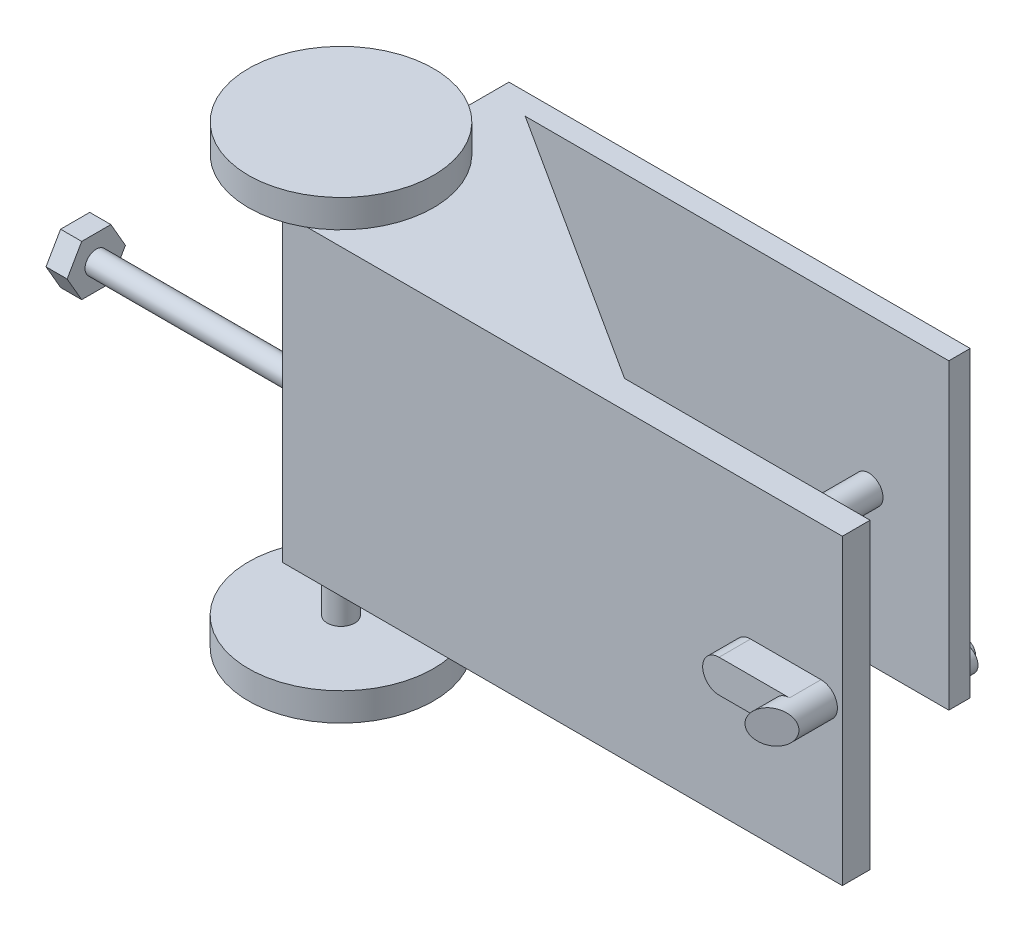
SolidWorks part; units mm, degrees
ref_plane "Plan de face" through (0, 0, 0) normal (0, 0, 1) x (1, 0, 0)
ref_plane "Plan de dessus" through (0, 0, 0) normal (0, 1, 0) x (1, 0, 0)
ref_plane "Plan de droite" through (0, 0, 0) normal (1, 0, 0) x (0, 0, -1)
sketch "Esquisse1" plane through (0, 0, 0) normal (0, 0, 1) x (1, 0, 0)
  line L0 (162.4526, 0) -> (162.4526, 87.2478)
  line L1 (162.4526, 0) -> (0.9932, 0)
  line L2 (162.4526, 87.2478) -> (0.9932, 87.2478)
  line L3 (0.9932, 0) -> (0.9932, 87.2478)
extrude "Boss.-Extru.1" add sketch "Esquisse1" along normal blind 8
sketch "Esquisse8" plane through (0, 87.2478, 0) normal (0, 1, 0) x (1, 0, 0)
  line L0 (0.9932, 0) -> (0.9932, 58.1232)
  line L1 (0.9932, 0) -> (91.6553, 0)
  line L2 (0.9932, 58.1232) -> (91.6553, 58.1232)
  line L3 (91.6553, 0) -> (91.6553, 58.1232)
  line L4 (0.9932, 58.1232) -> (91.6553, 0)
  line L5 (0.9932, 58.1232) -> (32.8752, 107.8536)
  line L6 (91.6553, 0) -> (123.5373, 49.7304)
  line L7 (32.8752, 107.8536) -> (123.5373, 49.7304)
  line M5 (162.4526, 0) -> (0.9932, 0)
extrude "Boss.-Extru.4" add sketch "Esquisse8" against normal blind 8 contours L4 L0 M5
sketch "Esquisse9" plane through (0, 79.2478, 0) normal (0, -1, 0) x (-1, 0, 0)
  line L0 (-0.9932, 58.1232) -> (-91.6553, 0)
  line L1 (-91.6553, 0) -> (-0.9932, 0)
  line L2 (-0.9932, 0) -> (-0.9932, 58.1232)
extrude "Boss.-Extru.5" add sketch "Esquisse9" along normal up to surface (79.2478 mm away) contours L2 L0 L1 up to face at (81.7229, 0, 4)
sketch "Esquisse10" plane through (0.9932, 0, 0) normal (-1, 0, 0) x (0, 0, 1)
  line L0 (0.0289, 80.9428) -> (0.0289, 6.4515)
  line L1 (0.0289, 80.9428) -> (-66.0841, 80.9428)
  line L2 (0.0289, 6.4515) -> (-66.0841, 6.4515)
  line L3 (-66.0841, 80.9428) -> (-66.0841, 6.4515)
extrude "Enlèv. mat.-Extru.2" cut sketch "Esquisse10" against normal blind 96
sketch "Esquisse13" plane through (0.9932, 0, 0) normal (-1, 0, 0) x (0, 0, 1)
  line L0 (-57.3293, 0) -> (-57.3293, 87.2478)
  line L1 (-57.3293, 0) -> (-51.1587, 0)
  line L2 (-57.3293, 87.2478) -> (-51.1587, 87.2478)
  line L3 (-51.1587, 0) -> (-51.1587, 87.2478)
  line L4 (8, 0) -> (-58.1232, 0) construction
  line L5 (8, 87.2478) -> (-58.1232, 87.2478) construction
extrude "Boss.-Extru.6" add sketch "Esquisse13" against normal blind 133 contours L0 L2 L3 L1
sketch "Esquisse16" plane through (0, 0, -57.3293) normal (0, 0, -1) x (-1, 0, 0)
  circle A0 centre (-110.9236, 43.6239) radius 4.0925
  dimension "D1" = 8.185
extrude "Boss.-Extru.8" add sketch "Esquisse16" against normal blind 61.0904
sketch "Esquisse18" plane through (0, 0, -57.3293) normal (0, 0, -1) x (-1, 0, 0)
  line L0 (-128.5715, 5.1557) -> (-108.0869, 5.1557) construction
  line L1 (-128.5715, 8.7286) -> (-108.0869, 8.7286)
  line L2 (-128.5715, 1.5828) -> (-108.0869, 1.5828)
  arc A0 (-128.5715, 8.7286) -> (-128.5715, 1.5828) centre (-128.5715, 5.1557) ccw
  arc A1 (-108.0869, 1.5828) -> (-108.0869, 8.7286) centre (-108.0869, 5.1557) ccw
  point P2 (-118.3292, 5.1557)
extrude "Boss.-Extru.9" add sketch "Esquisse18" along normal blind 4.0904
sketch "Esquisse20" plane through (0, 0, -61.4197) normal (0, 0, -1) x (-1, 0, 0)
  circle A0 centre (-126.4235, 5.1557) radius 2.9502
extrude "Boss.-Extru.11" add sketch "Esquisse20" along normal blind 2.0904
sketch "Esquisse22" plane through (0, 0, -61.4197) normal (0, 0, -1) x (-1, 0, 0)
  circle A0 centre (-119.4027, 5.1557) radius 2.9502
  dimension "D1" = 5.9005
extrude "Boss.-Extru.12" add sketch "Esquisse22" along normal blind 2.0904
sketch "Esquisse23" plane through (0, 0, -61.4197) normal (0, 0, -1) x (-1, 0, 0)
  circle A0 centre (-109.5748, 5.1557) radius 3.3991
extrude "Boss.-Extru.13" add sketch "Esquisse23" along normal blind 4.0904
sketch "Esquisse24" plane through (0, 87.2478, 0) normal (0, 1, 0) x (1, 0, 0)
  circle A0 centre (9.8998, 0) radius 3.9591
  dimension "D1" = 7.9182
extrude "Boss.-Extru.14" add sketch "Esquisse24" along normal blind 15.0904 and the other way blind 100
sketch "Esquisse25" plane through (0, 102.3382, 0) normal (0, 1, 0) x (1, 0, 0)
  circle A0 centre (9.8998, 0) radius 26.6848
  dimension "D1" = 53.3696
extrude "Boss.-Extru.15" add sketch "Esquisse25" along normal blind 8.0904
sketch "Esquisse26" plane through (0, -12.7522, 0) normal (0, -1, 0) x (-1, 0, 0)
  circle A0 centre (-9.8998, 0) radius 26.6848
  dimension "D1" = 53.3696
extrude "Boss.-Extru.16" add sketch "Esquisse26" along normal blind 8.0904
sketch "Esquisse27" plane through (0, 0, 8) normal (0, 0, 1) x (1, 0, 0)
  line L0 (156.3009, 43.6239) -> (135.9971, 43.6239) construction
  line L1 (156.3009, 38.8896) -> (135.9971, 38.8896)
  line L2 (156.3009, 48.3583) -> (135.9971, 48.3583)
  arc A0 (156.3009, 38.8896) -> (156.3009, 48.3583) centre (156.3009, 43.6239) ccw
  arc A1 (135.9971, 48.3583) -> (135.9971, 38.8896) centre (135.9971, 43.6239) ccw
  point P2 (146.149, 43.6239)
extrude "Boss.-Extru.17" add sketch "Esquisse27" along normal blind 9.0904
sketch "Esquisse28" plane through (0.9932, 0, 0) normal (-1, 0, 0) x (0, 0, 1)
  circle A0 centre (3.5623, 43.6972) radius 3.2413
extrude "bolt" add sketch "Esquisse28" along normal blind 58.0904
sketch "Esquisse29" plane through (0, 0, -57.3293) normal (0, 0, -1) x (-1, 0, 0)
  line L0 (-15.9568, 87.2478) -> (-0.9195, 87.2478)
  line L1 (-15.9568, 87.2478) -> (-15.9568, -8.0839)
  line L2 (-0.9195, 87.2478) -> (-0.9195, -8.0839)
  line L3 (-15.9568, -8.0839) -> (-0.9195, -8.0839)
  line L4 (-133.9932, 87.2478) -> (-2.2315, 87.2478) construction
extrude "Enlèv. mat.-Extru.4" cut sketch "Esquisse29" along normal blind 9.0904
sketch "Esquisse30" plane through (-57.0972, 0, 0) normal (-1, 0, 0) x (0, 0, 1)
  line L1 (11.9703, 43.6972) -> (7.7663, 50.9787)
  line L2 (7.7663, 50.9787) -> (-0.6417, 50.9787)
  line L3 (-0.6417, 50.9787) -> (-4.8457, 43.6972)
  line L4 (-4.8457, 43.6972) -> (-0.6417, 36.4156)
  line L5 (-0.6417, 36.4156) -> (7.7663, 36.4156)
  line L6 (7.7663, 36.4156) -> (11.9703, 43.6972)
  circle A0 centre (3.5623, 43.6972) radius 7.2816 construction
extrude "bolt 2" add sketch "Esquisse30" along normal blind 6.0904
sketch "Esquisse31" plane through (0, 0, 17.0904) normal (0, 0, 1) x (1, 0, 0)
  circle A0 centre (156.3009, 43.6239) radius 4.7343
extrude "Boss.-Extru.20" add sketch "Esquisse31" along normal blind 8.0904
sketch "Esquisse32" plane through (0, 48.3583, 0) normal (0, 1, 0) x (1, 0, 0)
  line L0 (151.5665, -25.1807) -> (161.0352, -19.0961)
  line L1 (151.5665, -25.1807) -> (155.1786, -30.8017)
  line L2 (161.0352, -19.0961) -> (164.6473, -24.7171)
  line L3 (155.1786, -30.8017) -> (164.6473, -24.7171)
  line L4 (161.0352, -25.1807) -> (161.0352, -8) construction
extrude "Enlèv. mat.-Extru.5" cut sketch "Esquisse32" against normal blind 11.0904
sketch "Esquisse34" plane through (0, 0, -57.3293) normal (0, 0, -1) x (-1, 0, 0)
  text T0 "Cake is a lie" font "Century Gothic" height in points 18
extrude "Enlèv. mat.-Extru.6" cut sketch "Esquisse34" against normal blind 1.0904
